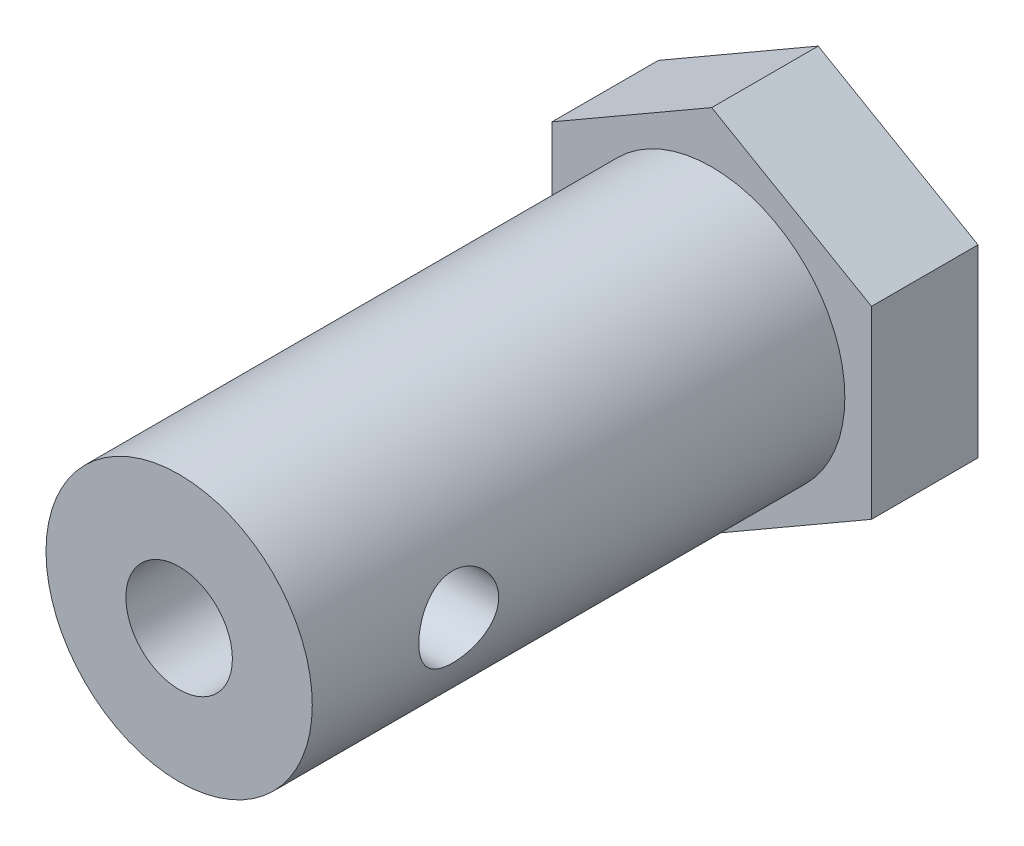
SolidWorks part; units mm, degrees
ref_plane "Front Plane" through (0, 0, 0) normal (0, 0, 1) x (1, 0, 0)
ref_plane "Top Plane" through (0, 0, 0) normal (0, 1, 0) x (1, 0, 0)
ref_plane "Right Plane" through (0, 0, 0) normal (1, 0, 0) x (0, 0, -1)
sketch "Sketch1" plane through (0, 0, 0) normal (0, 0, 1) x (1, 0, 0)
  line L1 (0, 6.9282) -> (-6, 3.4641)
  line L2 (-6, 3.4641) -> (-6, -3.4641)
  line L3 (-6, -3.4641) -> (0, -6.9282)
  line L4 (0, -6.9282) -> (6, -3.4641)
  line L5 (6, -3.4641) -> (6, 3.4641)
  line L6 (6, 3.4641) -> (0, 6.9282)
  circle A0 centre (0, 0) radius 6 construction
extrude "Boss-Extrude1" add sketch "Sketch1" along normal blind 4
sketch "Sketch2" plane through (0, 0, 4) normal (0, 0, 1) x (1, 0, 0)
  circle A0 centre (0, 0) radius 5
extrude "Boss-Extrude2" add sketch "Sketch2" along normal blind 20
sketch "Sketch3" plane through (0, 0, 24) normal (0, 0, 1) x (1, 0, 0)
  circle A0 centre (0, 0) radius 2
extrude "Cut-Extrude1" cut sketch "Sketch3" against normal blind 10
sketch "Sketch4" plane through (0, 0, 0) normal (1, 0, 0) x (0, 0, -1)
  line L0 (-24, 0) -> (-18.5, 0) construction
  line L1 (-24, 5) -> (-24, -5) construction
  circle A0 centre (-18.5, 0) radius 1.5
extrude "Cut-Extrude2" cut sketch "Sketch4" along normal blind 7
sketch "Sketch5" plane through (0, 0, 0) normal (0, 0, -1) x (-1, 0, 0)
  circle A0 centre (0, 0) radius 1.5
extrude "Cut-Extrude3" cut sketch "Sketch5" against normal blind 10
